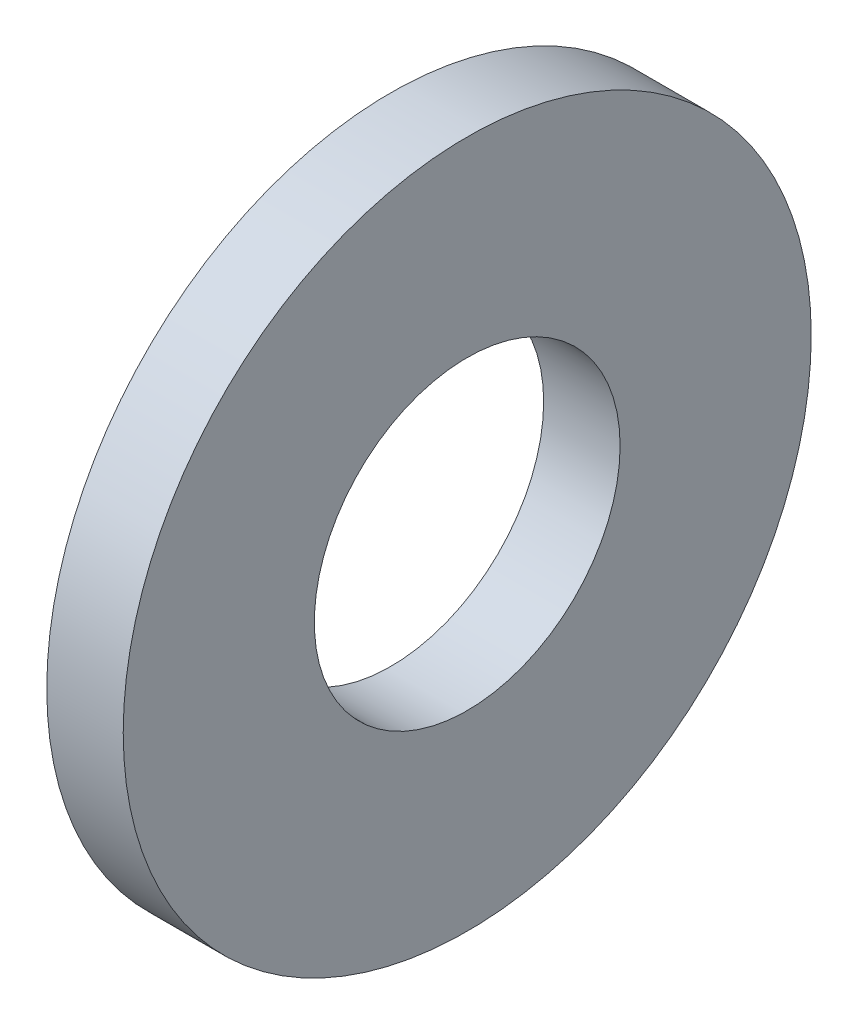
SolidWorks part; units mm, degrees
material "Pine"
ref_plane "Front Plane" through (0, 0, 0) normal (0, 0, 1) x (1, 0, 0)
ref_plane "Top Plane" through (0, 0, 0) normal (0, 1, 0) x (1, 0, 0)
ref_plane "Right Plane" through (0, 0, 0) normal (1, 0, 0) x (0, 0, -1)
sketch "Sketch1" plane through (0, 0, 0) normal (1, 0, 0) x (0, 0, -1)
  circle A0 centre (0, 0) radius 9
  dimension "D1" = 18
extrude "Boss-Extrude1" add sketch "Sketch1" along normal blind 2
sketch "Sketch2" plane through (2, 0, 0) normal (1, 0, 0) x (0, 0, -1)
  circle A2 centre (0, 0) radius 4
  dimension "D1" = 8
extrude "Cut-Extrude1" cut sketch "Sketch2" against normal through all
